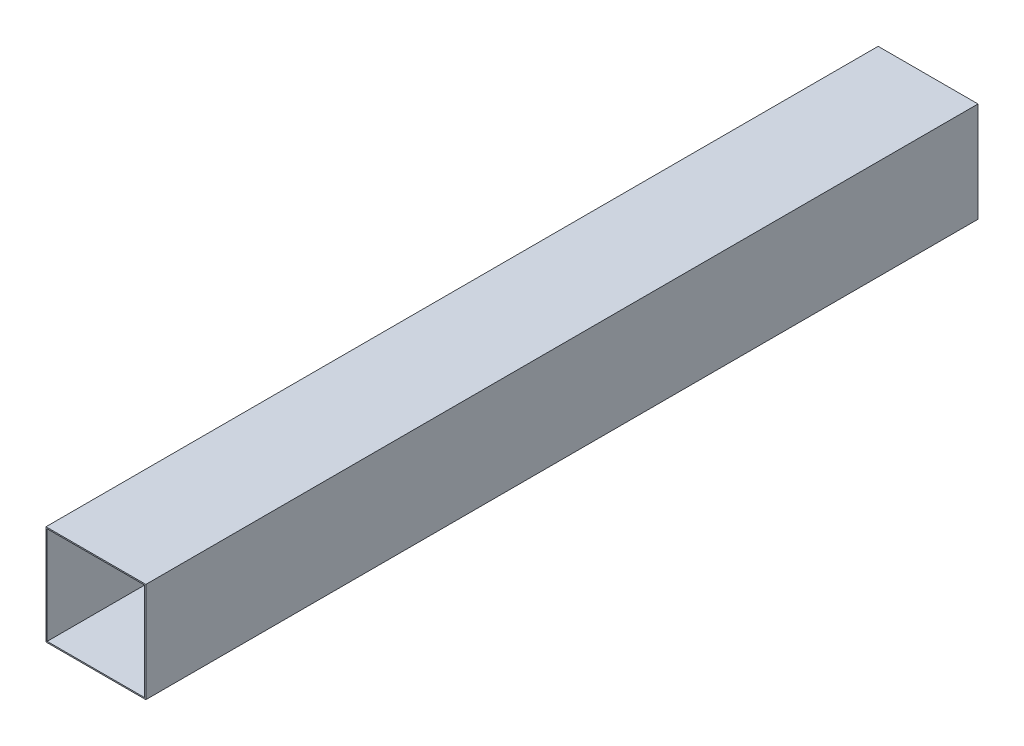
SolidWorks part; units mm, degrees
ref_plane "Front Plane" through (0, 0, 0) normal (0, 0, 1) x (1, 0, 0)
ref_plane "Top Plane" through (0, 0, 0) normal (0, 1, 0) x (1, 0, 0)
ref_plane "Right Plane" through (0, 0, 0) normal (1, 0, 0) x (0, 0, -1)
sketch "Sketch1" plane through (0, 0, 0) normal (0, 0, 1) x (1, 0, 0)
  line L1 (38.1, -38.1) -> (-38.1, -38.1)
  line L2 (38.1, -38.1) -> (38.1, 38.1)
  line L3 (38.1, 38.1) -> (-38.1, 38.1)
  line L4 (-38.1, -38.1) -> (-38.1, 38.1)
  line L5 (38.1, -38.1) -> (-38.1, 38.1) construction
  line L6 (38.1, 38.1) -> (-38.1, -38.1) construction
  line L7 (37.1856, -37.1856) -> (-37.1856, -37.1856)
  line L8 (37.1856, -37.1856) -> (37.1856, 37.1856)
  line L9 (37.1856, 37.1856) -> (-37.1856, 37.1856)
  line L10 (-37.1856, -37.1856) -> (-37.1856, 37.1856)
  line L11 (37.1856, -37.1856) -> (-37.1856, 37.1856) construction
  line L12 (37.1856, 37.1856) -> (-37.1856, -37.1856) construction
  point P0 (0, 0)
  point P6 (0, 0)
  dimension "D1" = 76.2
  dimension "D2" = 76.2
  dimension "D3" = 0.9144
extrude "Boss-Extrude1" add sketch "Sketch1" along normal blind 635 contours L4 L3 L2 L1 | L10 L9 L8 L7
ref_plane "Plane1" through (0, 0, 317.5) normal (0, 0, 1) x (1, 0, 0)
